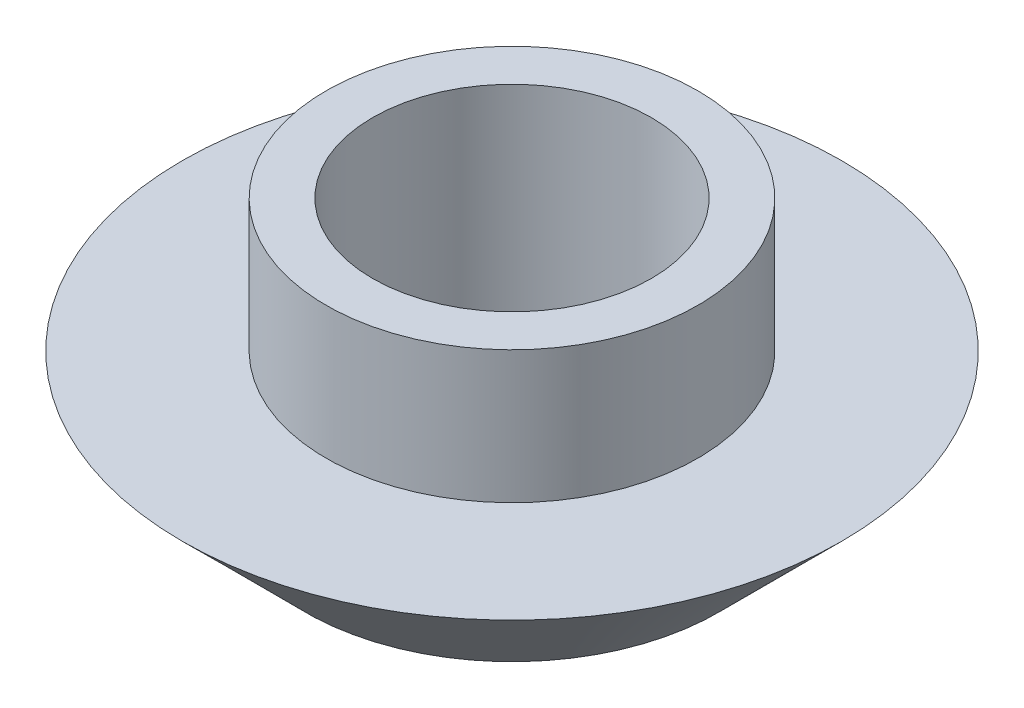
SolidWorks part; units mm, degrees
material "7075-T6 (SN)"
ref_plane "Płaszczyzna XY" through (0, 0, 0) normal (0, 0, 1) x (1, 0, 0)
ref_plane "Płaszczyzna XZ" through (0, 0, 0) normal (0, 1, 0) x (1, 0, 0)
ref_plane "Płaszczyzna YZ" through (0, 0, 0) normal (1, 0, 0) x (0, 0, -1)
sketch "Szkic1" plane through (0, 0, 0) normal (0, 0, 1) x (1, 0, 0)
  line L0 (0, 0) -> (0, 5.495)
  line L1 (0, 5.495) -> (4, 5.495)
  line L2 (4, 5.495) -> (4, 2.645)
  line L3 (4, 2.645) -> (7.095, 2.645)
  line L4 (7.095, 2.645) -> (4.45, 0)
  line L5 (4.45, 0) -> (0, 0)
  dimension "D1" = 4
  dimension "D2" = 2.85
  dimension "D3" = 2.645
  dimension "D4" = 4.45
  dimension "D5" = 45
revolve "Obrót1" add sketch "Szkic1" angle 360 about L0
hole_wizard "Otwory ustalające Ø6.0mm1" positions "Szkic2" profile "Szkic3" hole size "Ø6.0" standard "ISO" end condition through all
sketch "Szkic2" plane through (0, 5.495, 0) normal (0, 1, 0) x (1, 0, 0)
  point P0 (0, 0)
sketch "Szkic3" plane through (0, 5.495, 0) normal (1, 0, 0) x (0, 0, 1)
  line L0 (0, 0) -> (0, 5.495)
  line L1 (0, 5.495) -> (3, 5.495)
  line L2 (3, 5.495) -> (3, 0)
  line L5 (3, 0) -> (0, 0)
  line L11 (0, -6.35) -> (0, 107.95) construction
  dimension "Średnica otworu na wylot" = 6
  dimension "Głębokość otworu na wylot" = 5.495
